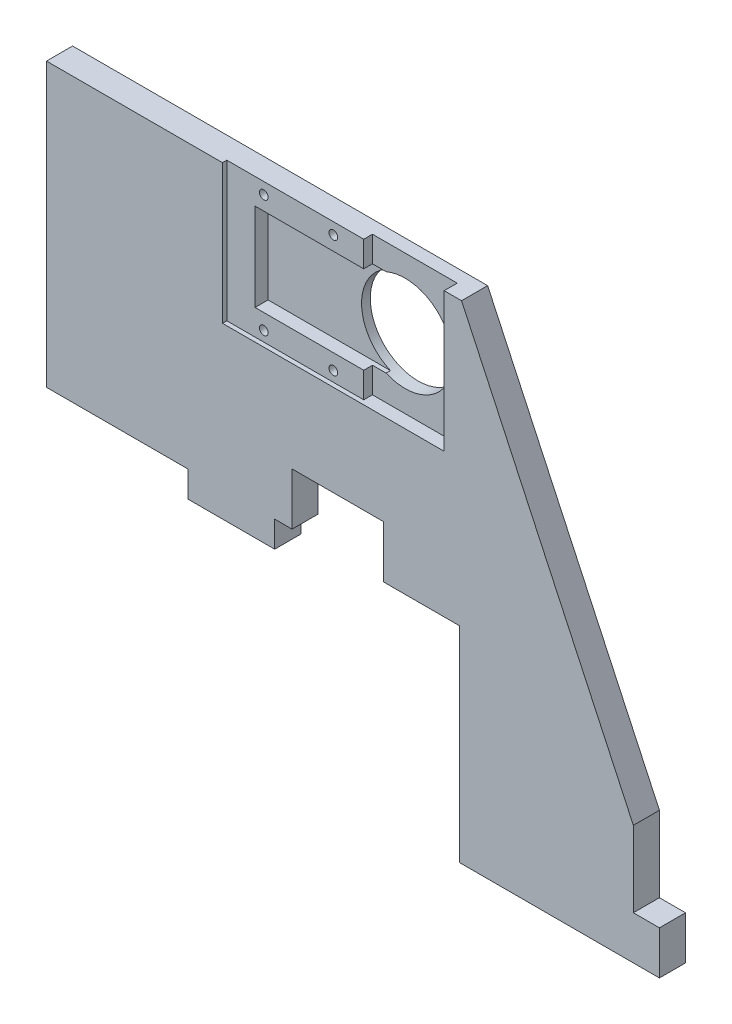
SolidWorks part; units mm, degrees
ref_plane "Plan de face" through (0, 0, 0) normal (0, 0, 1) x (1, 0, 0)
ref_plane "Plan de dessus" through (0, 0, 0) normal (0, 1, 0) x (1, 0, 0)
ref_plane "Plan de droite" through (0, 0, 0) normal (1, 0, 0) x (0, 0, -1)
sketch "Esquisse1" plane through (0, 0, 0) normal (0, 0, 1) x (1, 0, 0)
  line L1 (-67.5, 56.085) -> (67.5, 56.085)
  line L2 (-67.5, 56.085) -> (-67.5, -56.085)
  line L3 (-67.5, -56.085) -> (67.5, -56.085)
  line L4 (67.5, 56.085) -> (67.5, -56.085)
  dimension "D1" = 135
  dimension "D2" = 112.17
  dimension "D3" = 67.5
  dimension "D4" = 56.085
extrude "Boss.-Extru.1" add sketch "Esquisse1" along normal blind 6
sketch "Esquisse2" plane through (0, 0, 6) normal (0, 0, 1) x (1, 0, 0)
  line L0 (-67.5, -56.085) -> (67.5, -56.085) construction
  line L1 (27.5, -56.085) -> (-67.5, -56.085)
  line L2 (27.5, -56.085) -> (27.5, -8.915)
  line L3 (-38.5, -8.915) -> (27.5, -8.915)
  line L4 (-67.5, -56.085) -> (-67.5, -8.915)
  line L5 (-67.5, 56.085) -> (-67.5, -56.085) construction
  line L7 (67.5, -28.665) -> (27.9804, 56.085)
  line L8 (-38.5, -8.915) -> (-67.5, -8.915)
  line L9 (67.5, -56.085) -> (67.5, 56.085) construction
  line L10 (67.5, 56.085) -> (-67.5, 56.085) construction
  line L11 (27.9804, 56.085) -> (67.5, 56.085)
  line L12 (67.5, 56.085) -> (67.5, -28.665)
  dimension "D1" = 47.17
  dimension "D2" = 95
  dimension "D3" = 27.42
  dimension "D4" = 155
  dimension "D5" = 115
extrude "Enlèv. mat.-Extru.1" cut sketch "Esquisse2" against normal blind 6
sketch "Esquisse3" plane through (0, 0, 6) normal (0, 0, 1) x (1, 0, 0)
  line L0 (67.5, -56.085) -> (67.5, -28.665) construction
  line L1 (67.5, -56.085) -> (73.5, -56.085)
  line L2 (67.5, -56.085) -> (67.5, -46.085)
  line L3 (67.5, -46.085) -> (73.5, -46.085)
  line L4 (73.5, -56.085) -> (73.5, -46.085)
  line L6 (-35, -8.915) -> (-15, -8.915)
  line L7 (-35, -8.915) -> (-35, -14.915)
  line L8 (-35, -14.915) -> (-15, -14.915)
  line L9 (-15, -8.915) -> (-15, -14.915)
  line L10 (27.5, -8.915) -> (-67.5, -8.915) construction
  line L16 (27.5, -56.085) -> (27.5, -8.915) construction
  dimension "D3" = 6
  dimension "D4" = 20
  dimension "D5" = 42.5
  dimension "D6" = 10
  dimension "D7" = 6
extrude "Boss.-Extru.2" add sketch "Esquisse3" against normal blind 6
sketch "Esquisse4" plane through (0, 0, 6) normal (0, 0, 1) x (1, 0, 0)
  line L0 (27.9804, 56.085) -> (-67.5, 56.085) construction
  line L1 (-27.0196, 56.085) -> (23.9804, 56.085)
  line L2 (-27.0196, 56.085) -> (-27.0196, 24.085)
  line L3 (-27.0196, 24.085) -> (23.9804, 24.085)
  line L4 (23.9804, 56.085) -> (23.9804, 24.085)
  dimension "D1" = 51
  dimension "D2" = 32
  dimension "D3" = 4
  dimension "D4" = 0
extrude "Enlèv. mat.-Extru.2" cut sketch "Esquisse4" against normal blind 3
sketch "Esquisse5" plane through (0, 0, 3) normal (0, 0, 1) x (1, 0, 0)
  line L0 (23.9804, 24.085) -> (23.9804, 56.085) construction
  line L1 (23.9804, 56.085) -> (-27.0196, 56.085) construction
  circle A0 centre (11.9804, 40.085) radius 11
  point P2 (23.9804, 40.085)
  dimension "D1" = 22
  dimension "D2" = 12
  dimension "D3" = 16
extrude "Enlèv. mat.-Extru.3" cut sketch "Esquisse5" against normal through all
sketch "Esquisse6" plane through (0, 0, 3) normal (0, 0, 1) x (1, 0, 0)
  line L1 (-20.5196, 50.185) -> (9.4804, 50.185)
  line L2 (-20.5196, 50.185) -> (-20.5196, 29.985)
  line L3 (-20.5196, 29.985) -> (9.4804, 29.985)
  line L4 (9.4804, 50.185) -> (9.4804, 29.985)
  circle A0 centre (11.9804, 40.085) radius 11 construction
  dimension "D1" = 30
  dimension "D2" = 20.2
  dimension "D3" = 10.1
  dimension "D4" = 32.5
extrude "Enlèv. mat.-Extru.4" cut sketch "Esquisse6" against normal blind 1
sketch "Esquisse7" plane through (0, 0, 3) normal (0, 0, 1) x (1, 0, 0)
  line L0 (23.9804, 56.085) -> (-27.0196, 56.085) construction
  line L1 (4.4804, 56.085) -> (-20.5196, 56.085)
  line L2 (4.4804, 56.085) -> (4.4804, 50.185)
  line L3 (4.4804, 50.185) -> (-20.5196, 50.185)
  line L4 (-20.5196, 56.085) -> (-20.5196, 50.185)
  dimension "D1" = 25
extrude "Boss.-Extru.3" add sketch "Esquisse7" along normal blind 2
sketch "Esquisse8" plane through (0, 0, 3) normal (0, 0, 1) x (1, 0, 0)
  line L1 (-27.0196, 24.085) -> (23.9804, 24.085) construction
  line L2 (-20.5196, 29.985) -> (4.4804, 29.985)
  line L3 (-20.5196, 29.985) -> (-20.5196, 24.085)
  line L4 (-20.5196, 24.085) -> (4.4804, 24.085)
  line L5 (4.4804, 29.985) -> (4.4804, 24.085)
  dimension "D1" = 25
extrude "Boss.-Extru.4" add sketch "Esquisse8" along normal blind 2
sketch "Esquisse9" plane through (0, 0, 3) normal (0, 0, 1) x (1, 0, 0)
  line L1 (-27.0196, 56.085) -> (-20.5196, 56.085)
  line L2 (-27.0196, 56.085) -> (-27.0196, 24.085)
  line L3 (-27.0196, 24.085) -> (-20.5196, 24.085)
  line L4 (-20.5196, 56.085) -> (-20.5196, 24.085)
extrude "Boss.-Extru.5" add sketch "Esquisse9" along normal blind 2
sketch "Esquisse10" plane through (0, 0, 5) normal (0, 0, 1) x (1, 0, 0)
  line L0 (-27.0196, 56.085) -> (-27.0196, 24.085) construction
  line L1 (-27.0196, 56.085) -> (-27.0196, 24.085) construction
  line L4 (4.4804, 56.085) -> (-27.0196, 56.085) construction
  line L6 (-20.5196, 29.985) -> (7.6227, 29.985) construction
  circle A0 centre (-18.5196, 53.435) radius 1
  circle A1 centre (-2.5196, 53.435) radius 1
  circle A2 centre (-18.5196, 26.435) radius 1
  circle A3 centre (-2.5196, 26.435) radius 1
  dimension "D1" = 2
  dimension "D2" = 2
  dimension "D3" = 8.5
  dimension "D4" = 16
  dimension "D5" = 2
  dimension "D6" = 2
  dimension "D9" = 2.65
  dimension "D10" = 3.55
  dimension "D11" = 2.65
  dimension "D12" = 3.55
  dimension "D7" = 16
  dimension "D8" = 8.5
extrude "Enlèv. mat.-Extru.5" cut sketch "Esquisse10" against normal through all
sketch "Esquisse11" plane through (0, 0, 6) normal (0, 0, 1) x (1, 0, 0)
  line L0 (27.5, -8.915) -> (-15, -8.915) construction
  line L1 (-11, -8.915) -> (10, -8.915)
  line L2 (-11, -8.915) -> (-11, 3.085)
  line L3 (-11, 3.085) -> (10, 3.085)
  line L4 (10, -8.915) -> (10, 3.085)
  line L5 (-67.5, 56.085) -> (-67.5, -8.915) construction
  dimension "D1" = 12
  dimension "D2" = 21
  dimension "D3" = 56.5
extrude "Enlèv. mat.-Extru.6" cut sketch "Esquisse11" against normal blind 6
equation "\"D3@Esquisse1\"=\"D1@Esquisse1\"/2"
equation "\"D4@Esquisse1\"=\"D2@Esquisse1\"/2"
